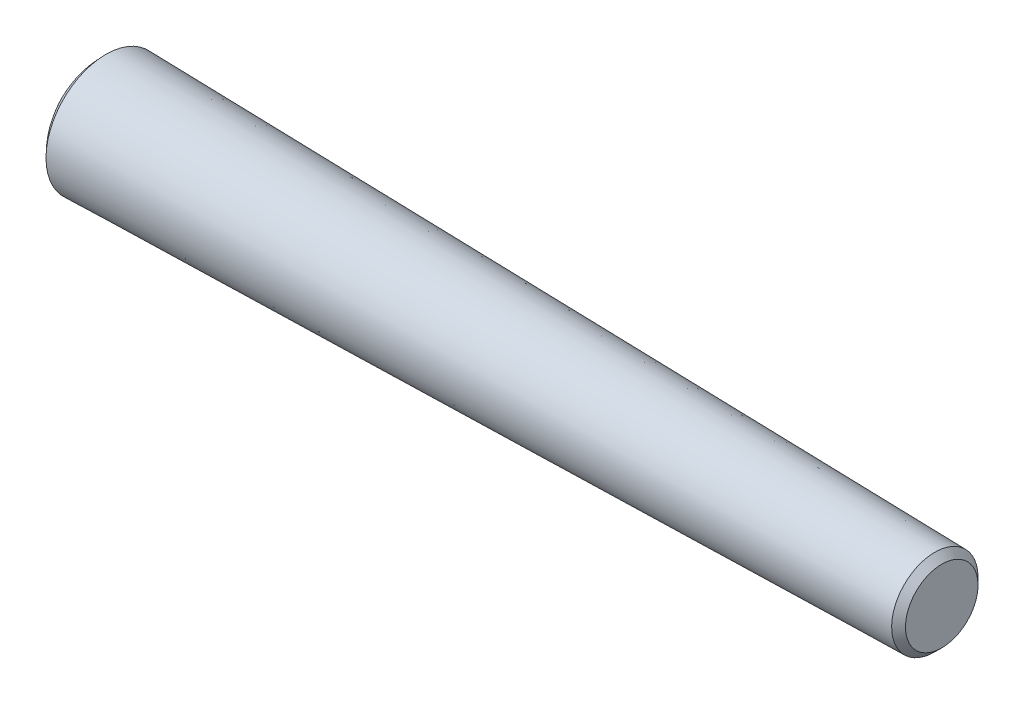
SolidWorks part; units mm, degrees
ref_plane "Front Plane" through (0, 0, 0) normal (0, 0, 1) x (1, 0, 0)
ref_plane "Top Plane" through (0, 0, 0) normal (0, 1, 0) x (1, 0, 0)
ref_plane "Right Plane" through (0, 0, 0) normal (1, 0, 0) x (0, 0, -1)
sketch "Sketch1" plane through (0, 0, 0) normal (0, 0, 1) x (1, 0, 0)
  line L0 (0, 0) -> (12, 0) construction
  line L1 (0, 0.8659) -> (12, 0.625)
  line L2 (0, 0) -> (-0.3692, 0) construction
  line L3 (0, 0.8659) -> (0, 0) construction
  line L5 (12, 0.625) -> (12.1, 0.525)
  line L6 (12.1, 0.525) -> (12.1, 0)
  line L7 (-0.3692, 0) -> (12.1, 0)
  line L8 (12, 0.625) -> (12.3394, 0.625) construction
  arc A0 (0, 0.8659) -> (-0.3692, 0) centre (0.8308, 0) ccw
  dimension "D6" = 1.2
  dimension "D1" = 0.625
  dimension "D2" = 12
  dimension "D3" = 1.15
  dimension "D4" = 0.1
  dimension "D5" = 45
revolve "Revolve2" add sketch "Sketch1" angle 360 about L7
